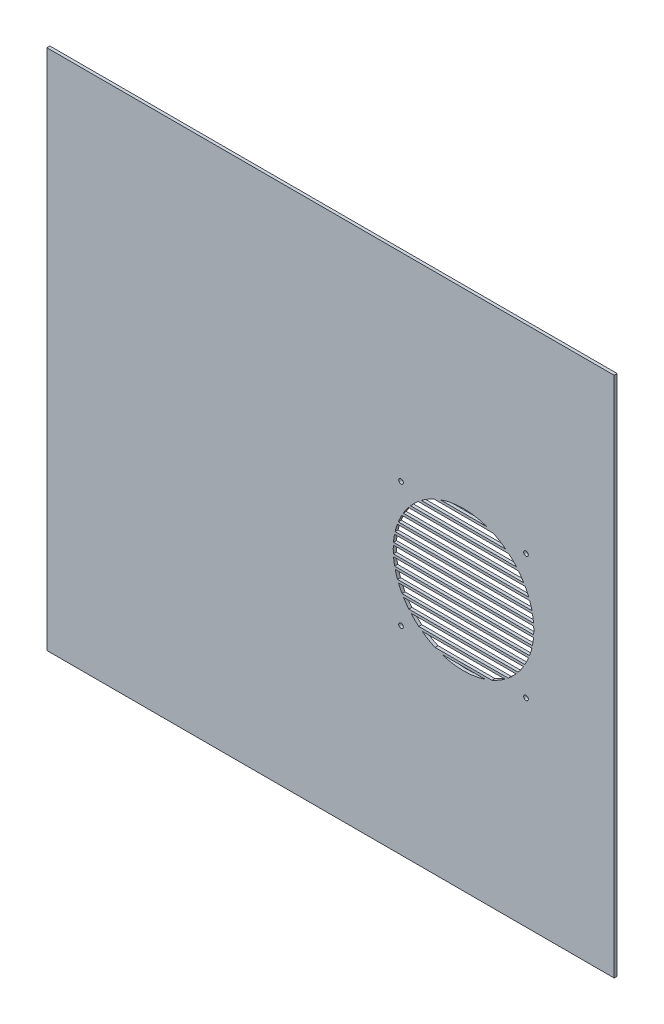
SolidWorks part; units mm, degrees
ref_plane "Přední rovina" through (0, 0, 0) normal (0, 0, 1) x (1, 0, 0)
ref_plane "Horní rovina" through (0, 0, 0) normal (0, 1, 0) x (1, 0, 0)
ref_plane "Pravá rovina" through (0, 0, 0) normal (1, 0, 0) x (0, 0, -1)
sketch "Skica1" plane through (0, 0, 0) normal (0, 0, 1) x (1, 0, 0)
  line L0 (213.2108, -56.5) -> (38.8643, -56.5)
  line L1 (-282.5, 260) -> (282.5, 260)
  line L2 (-282.5, 260) -> (-282.5, -260)
  line L3 (-282.5, -260) -> (282.5, -260)
  line L4 (282.5, 260) -> (282.5, -260)
  line L5 (-282.5, 260) -> (282.5, -260) construction
  line L6 (-282.5, -260) -> (282.5, 260) construction
  line L7 (213.2108, -66.5) -> (38.8643, -66.5)
  line L8 (213.2108, -66.5) -> (213.2108, -64)
  line L9 (213.2108, -64) -> (38.8643, -64)
  line L10 (38.8643, -66.5) -> (38.8643, -64)
  line L11 (213.2108, -54) -> (38.8643, -54)
  line L12 (213.2108, -56.5) -> (213.2108, -54)
  line L13 (38.8643, -56.5) -> (38.8643, -54)
  line L14 (213.2108, -46.5) -> (38.8643, -46.5)
  line L15 (213.2108, -44) -> (38.8643, -44)
  line L16 (213.2108, -46.5) -> (213.2108, -44)
  line L17 (38.8643, -46.5) -> (38.8643, -44)
  line L18 (213.2108, -36.5) -> (38.8643, -36.5)
  line L19 (213.2108, -34) -> (38.8643, -34)
  line L20 (213.2108, -36.5) -> (213.2108, -34)
  line L21 (38.8643, -36.5) -> (38.8643, -34)
  line L22 (213.2108, -26.5) -> (38.8643, -26.5)
  line L23 (213.2108, -24) -> (38.8643, -24)
  line L24 (213.2108, -26.5) -> (213.2108, -24)
  line L25 (38.8643, -26.5) -> (38.8643, -24)
  line L26 (213.2108, -16.5) -> (38.8643, -16.5)
  line L27 (213.2108, -14) -> (38.8643, -14)
  line L28 (213.2108, -16.5) -> (213.2108, -14)
  line L29 (38.8643, -16.5) -> (38.8643, -14)
  line L30 (213.2108, -6.5) -> (38.8643, -6.5)
  line L31 (213.2108, -4) -> (38.8643, -4)
  line L32 (213.2108, -6.5) -> (213.2108, -4)
  line L33 (38.8643, -6.5) -> (38.8643, -4)
  line L34 (213.2108, 3.5) -> (38.8643, 3.5)
  line L35 (213.2108, 6) -> (38.8643, 6)
  line L36 (213.2108, 3.5) -> (213.2108, 6)
  line L37 (38.8643, 3.5) -> (38.8643, 6)
  line L38 (213.2108, 13.5) -> (38.8643, 13.5)
  line L39 (213.2108, 16) -> (38.8643, 16)
  line L40 (213.2108, 13.5) -> (213.2108, 16)
  line L41 (38.8643, 13.5) -> (38.8643, 16)
  line L42 (213.2108, 23.5) -> (38.8643, 23.5)
  line L43 (213.2108, 26) -> (38.8643, 26)
  line L44 (213.2108, 23.5) -> (213.2108, 26)
  line L45 (38.8643, 23.5) -> (38.8643, 26)
  line L46 (213.2108, 33.5) -> (38.8643, 33.5)
  line L47 (213.2108, 36) -> (38.8643, 36)
  line L48 (213.2108, 33.5) -> (213.2108, 36)
  line L49 (38.8643, 33.5) -> (38.8643, 36)
  line L50 (213.2108, 43.5) -> (38.8643, 43.5)
  line L51 (213.2108, 46) -> (38.8643, 46)
  line L52 (213.2108, 43.5) -> (213.2108, 46)
  line L53 (38.8643, 43.5) -> (38.8643, 46)
  line L54 (213.2108, 53.5) -> (38.8643, 53.5)
  line L55 (213.2108, 56) -> (38.8643, 56)
  line L56 (213.2108, 53.5) -> (213.2108, 56)
  line L57 (38.8643, 53.5) -> (38.8643, 56)
  line L58 (213.2108, 63.5) -> (38.8643, 63.5)
  line L59 (213.2108, 66) -> (38.8643, 66)
  line L60 (213.2108, 63.5) -> (213.2108, 66)
  line L61 (38.8643, 63.5) -> (38.8643, 66)
  circle A0 centre (132.5, 0) radius 70
  circle A1 centre (194.75, -62.25) radius 2.3
  circle A2 centre (70.25, -62.25) radius 2.3
  circle A3 centre (70.25, 62.25) radius 2.3
  circle A4 centre (194.75, 62.25) radius 2.3
  point P0 (0, 0)
  point P19 (132.5, 0)
  dimension "D3" = 140
  dimension "D5" = 4.6
  dimension "D6" = 62.25
  dimension "D7" = 62.25
  dimension "D1" = 565
  dimension "D2" = 520
  dimension "D4" = 150
  dimension "D9" = 2.5
  dimension "D10" = 66.5
  dimension "D11" = 14
  dimension "D8" = 4
extrude "Přidat vysunutím1" add sketch "Skica1" along normal blind 3 contours L4 L1 L2 L3 A4 L58 A0 L55 L56 L54 L51 L52 L50 L47 L48 L46 L43 L44 L42 L39 L40 L38 L35 L36 L34 L31 L32 L30 L27 L28 L26 L23 L24 L22 L19 L20 L18 L15 L16 L14 | A1 L9 A0 L7 L8 | L9 A0 L7 | A2 L9 L10 L7 A0 | A4 L58 L60 L59 A0 | L58 A0 L59 | A3 L58 A0 L59 L61 | L0 L13 L11 L12
